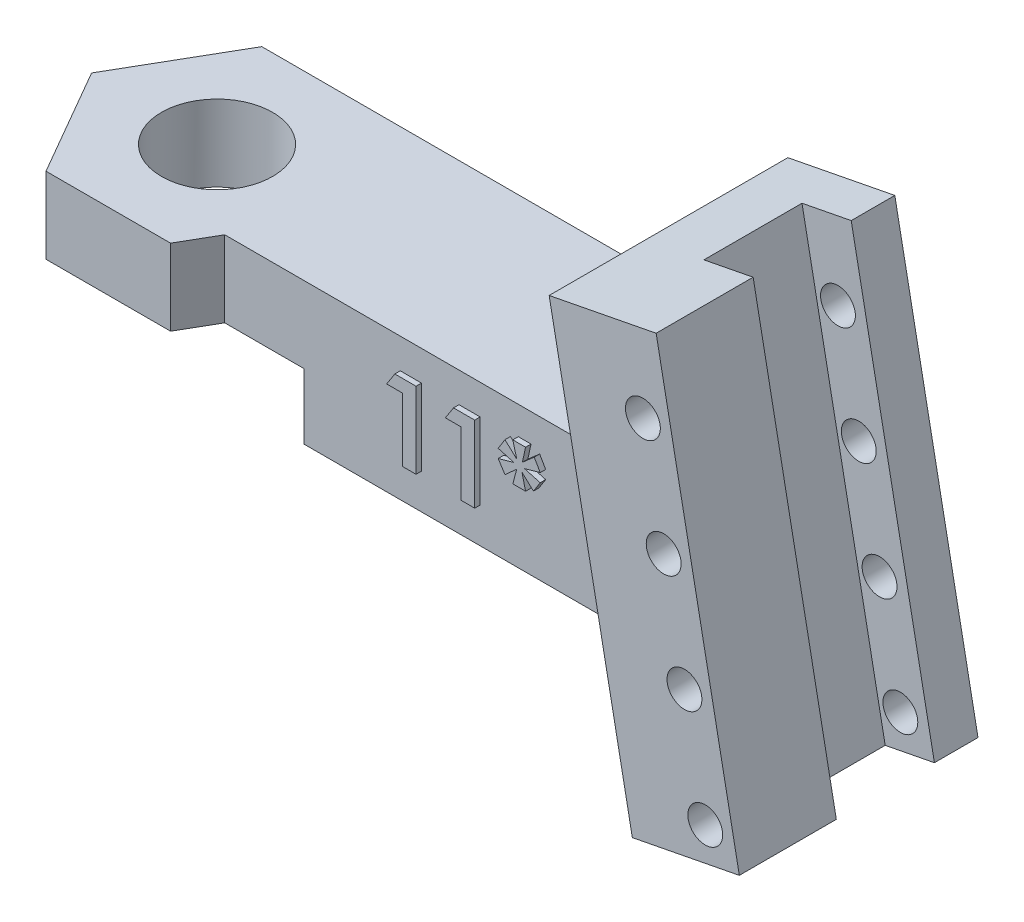
SolidWorks part; units mm, degrees
ref_plane "Front Plane" through (0, 0, 0) normal (0, 0, 1) x (1, 0, 0)
ref_plane "Top Plane" through (0, 0, 0) normal (0, 1, 0) x (1, 0, 0)
ref_plane "Right Plane" through (0, 0, 0) normal (1, 0, 0) x (0, 0, -1)
sketch "Sketch1" plane through (0, 0, 0) normal (0, 1, 0) x (1, 0, 0)
  line L1 (0, 0) -> (25, 0)
  line L2 (0, 0) -> (0, -6.75)
  line L3 (0, -6.75) -> (25, -6.75)
  line L4 (25, 0) -> (25, -6.75)
  dimension "D1" = 6.75
  dimension "D2" = 25
extrude "Boss-Extrude1" add sketch "Sketch1" along normal blind 6.5
ref_plane "Plane1" through (0, 0, 3.375) normal (0, 0, 1) x (1, 0, 0)
sketch "Sketch5" plane through (0, 6.5, 0) normal (0, 1, 0) x (1, 0, 0)
  line L0 (0, 0) -> (0, -6.75) construction
  line L1 (-5.7158, -3.375) -> (-2.8579, -8.325)
  line L2 (-2.8579, -8.325) -> (2.8579, -8.325)
  line L3 (2.8579, -8.325) -> (5.7158, -3.375)
  line L4 (5.7158, -3.375) -> (2.8579, 1.575)
  line L5 (2.8579, 1.575) -> (-2.8579, 1.575)
  line L6 (-2.8579, 1.575) -> (-5.7158, -3.375)
  circle A0 centre (0, -3.375) radius 4.95 construction
  dimension "D1" = 4.95
extrude "Boss-Extrude4" add sketch "Sketch5" against normal up to surface (6.5 mm away) up to face at (12.5, 0, 3.375)
sketch "Sketch3" plane through (0, 0, 3.375) normal (0, 0, 1) x (1, 0, 0)
  line L0 (21.2757, 14.1555) -> (26.1838, 15.1096)
  line L1 (26.1838, 15.1096) -> (30, -4.523)
  line L2 (30, -4.523) -> (25.0919, -5.477)
  line L3 (25.0919, -5.477) -> (21.2757, 14.1555)
  line L4 (3.7672, 6.5) -> (25, 6.5) construction
  point P6 (27.5459, -5)
  dimension "D1" = 30
  dimension "D2" = 5
  dimension "D3" = 20
  dimension "D4" = 79
  dimension "D6" = 5
extrude "Boss-Extrude3" add sketch "Sketch3" against normal up to surface (4.95 mm away) and the other way blind 6 up to face at (0, 3.25, -1.575)
sketch "Sketch4" plane through (-1.8768, 9.6551, 0) normal (-0.1908, 0.9816, 0) x (0.9816, 0.1908, 0)
  line L0 (28.5858, -9.375) -> (28.5858, 1.575) construction
  line L1 (26.2858, -0.425) -> (28.5858, -0.425)
  line L2 (26.2858, -0.425) -> (26.2858, -4.925)
  line L3 (26.2858, -4.925) -> (28.5858, -4.925)
  line L4 (28.5858, -0.425) -> (28.5858, -4.925)
  line L6 (28.5858, 1.575) -> (23.5858, 1.575) construction
  dimension "D1" = 4.5
  dimension "D2" = 2.3
  dimension "D3" = 2
extrude "Cut-Extrude1" cut sketch "Sketch4" against normal blind 23 contours L2 L3 L4 L1
sketch "Sketch6" plane through (0, 6.5, 0) normal (0, 1, 0) x (1, 0, 0)
  circle A0 centre (0, -3.3356) radius 2.55
  dimension "D1" = 5.1
extrude "Cut-Extrude2" cut sketch "Sketch6" against normal blind 10
sketch "Sketch7" plane through (0, 0, -1.575) normal (0, 0, -1) x (-1, 0, 0)
  line L0 (-2.8579, 0) -> (-24.0272, 0)
  line L1 (-24.0272, 0) -> (-25.0919, -5.477)
  line L2 (-25.0919, -5.477) -> (-30, -4.523)
  line L3 (-30, -4.523) -> (-26.1838, 15.1096)
  line L4 (-26.1838, 15.1096) -> (-21.2757, 14.1555)
  line L5 (-21.2757, 14.1555) -> (-22.7638, 6.5)
  line L6 (-22.7638, 6.5) -> (-2.8579, 6.5)
  line L7 (-2.8579, 6.5) -> (-2.8579, 0)
  dimension "D1" = 20
extrude "Boss-Extrude5" add sketch "Sketch7" against normal up to surface (1.575 mm away) up to face at (13.5814, 3.25, 0)
sketch "Sketch8" plane through (0, 0, 0) normal (0, -1, 0) x (-1, 0, 0)
  line L1 (-4.6765, -11.475) -> (4.6765, -11.475)
  line L2 (4.6765, -11.475) -> (9.3531, -3.375)
  line L3 (9.3531, -3.375) -> (4.6765, 4.725)
  line L4 (4.6765, 4.725) -> (-4.6765, 4.725)
  line L5 (-4.6765, 4.725) -> (-9.3531, -3.375)
  line L6 (-9.3531, -3.375) -> (-4.6765, -11.475)
  circle A0 centre (0, -3.375) radius 8.1 construction
  dimension "D1" = 16.2
extrude "Cut-Extrude3" cut sketch "Sketch8" against normal blind 3
sketch "Sketch9" plane through (0, 0, -1.575) normal (0, 0, -1) x (-1, 0, 0)
  line L0 (-30, -4.523) -> (-26.1838, 15.1096) construction
  line L1 (-25.0919, -5.477) -> (-30, -4.523) construction
  line L2 (-28.4377, -3.2986) -> (-25.5755, 11.4258) construction
  line L3 (-30, -4.523) -> (-26.1838, 15.1096) construction
  circle A0 centre (-28.4377, -3.2986) radius 0.8
  circle A4 centre (-27.4836, 1.6095) radius 0.8
  circle A5 centre (-26.5296, 6.5177) radius 0.8
  circle A6 centre (-25.5755, 11.4258) radius 0.8
  point P6 (0, 0)
  point P7 (0, 0)
  point P14 (0, 0)
  point P15 (-25.5861, 11.3628)
  dimension "D1" = 1.6
  dimension "D2" = 1.3
  dimension "D5" = 5
  dimension "D3" = 1.5
  dimension "D4" = 5
  dimension "D6" = 5
extrude "Cut-Extrude4" cut sketch "Sketch9" against normal up to surface (10.95 mm away) up to face at (25.6378, 4.8163, 9.375)
sketch "Sketch10" plane through (0, 0, 6.75) normal (0, 0, 1) x (1, 0, 0)
  text T0 "<b>11*</b>"
extrude "Boss-Extrude6" add sketch "Sketch10" along normal blind 0.25
